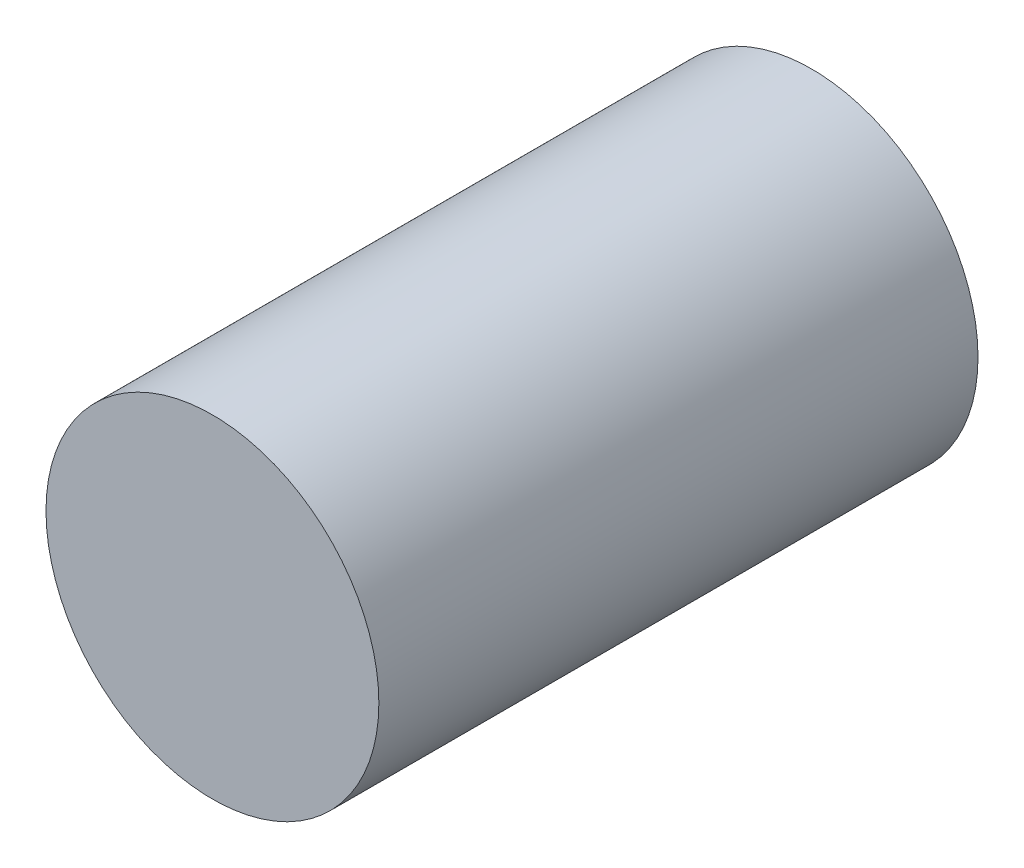
SolidWorks part; units mm, degrees
ref_plane "Front" through (0, 0, 0) normal (0, 0, 1) x (1, 0, 0)
ref_plane "Top" through (0, 0, 0) normal (0, 1, 0) x (1, 0, 0)
ref_plane "Right" through (0, 0, 0) normal (1, 0, 0) x (0, 0, -1)
sketch "Sketch1" plane through (0, 0, 0) normal (0, 0, 1) x (1, 0, 0)
  circle A0 centre (0, 0) radius 5
  arc A1 (4.0782, -2.8928) -> (-4.0782, 2.8928) centre (0, 0) ccw construction
extrude "Boss-Extrude1" add sketch "Sketch1" along normal mid plane 18
